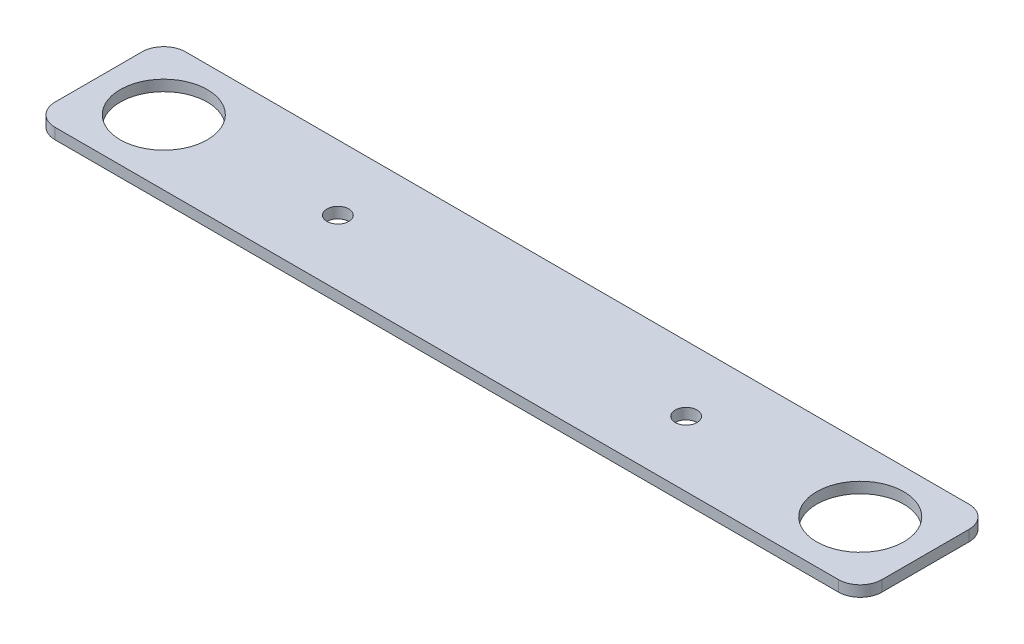
SolidWorks part; units mm, degrees
ref_plane "Front" through (0, 0, 0) normal (0, 0, 1) x (1, 0, 0)
ref_plane "Top" through (0, 0, 0) normal (0, 1, 0) x (1, 0, 0)
ref_plane "Right" through (0, 0, 0) normal (1, 0, 0) x (0, 0, -1)
sketch "Sketch1" plane through (0, 0, 0) normal (0, 1, 0) x (1, 0, 0)
  line L0 (0, 0) -> (203.2, 0) construction
  line L2 (-12.7, -19.05) -> (215.9, -19.05)
  line L3 (-19.05, -12.7) -> (-19.05, 12.7)
  line L4 (-12.7, 19.05) -> (215.9, 19.05)
  line L5 (222.25, -12.7) -> (222.25, 12.7)
  line L6 (-19.05, -19.05) -> (222.25, 19.05) construction
  line L7 (-19.05, 19.05) -> (222.25, -19.05) construction
  circle A0 centre (0, 0) radius 12.7
  circle A1 centre (203.2, 0) radius 12.7
  arc A2 (215.9, -19.05) -> (222.25, -12.7) centre (215.9, -12.7) ccw
  arc A3 (215.9, 19.05) -> (222.25, 12.7) centre (215.9, 12.7) cw
  arc A4 (-19.05, 12.7) -> (-12.7, 19.05) centre (-12.7, 12.7) cw
  arc A5 (-12.7, -19.05) -> (-19.05, -12.7) centre (-12.7, -12.7) cw
  circle A7 centre (50.8, 0) radius 3.175
  circle A8 centre (152.4, 0) radius 3.175
  point P5 (101.6, 0)
  point P22 (222.25, 0)
  dimension "D1" = 25.4
  dimension "D2" = 203.2
  dimension "D4" = 6.35
  dimension "D6" = 6.35
  dimension "D7" = 50.8
  dimension "D3" = 38.1
  dimension "D5" = 241.3
  dimension "D8" = 50.8
extrude "Boss-Extrude1" add sketch "Sketch1" along normal blind 3.175
